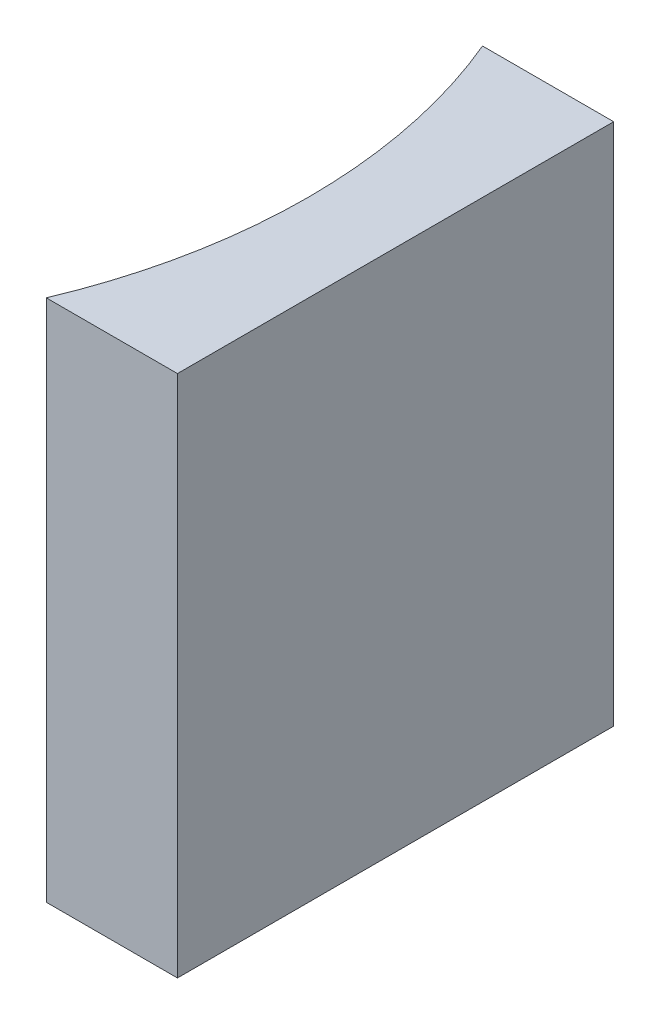
SolidWorks part; units mm, degrees
ref_plane "前视基准面" through (0, 0, 0) normal (0, 0, 1) x (1, 0, 0)
ref_plane "上视基准面" through (0, 0, 0) normal (0, 1, 0) x (1, 0, 0)
ref_plane "右视基准面" through (0, 0, 0) normal (1, 0, 0) x (0, 0, -1)
sketch "草图1" plane through (0, 0, 0) normal (0, 1, 0) x (1, 0, 0)
  line L0 (0, 0) -> (0, -10)
  line L1 (0, 0) -> (-3.0059, 0)
  line L2 (0, -10) -> (-3.0059, -10)
  line L3 (8.2336, -5) -> (-10.4405, -5) construction
  arc A0 (-3.0059, -10) -> (-3.0059, 0) centre (-14.93, -5) ccw
  point P7 (-2, -5)
  point P8 (0, -5)
  dimension "D2" = 12.93
  dimension "D3" = 2
  dimension "D1" = 10
extrude "凸台-拉伸1" add sketch "草图1" along normal blind 12
